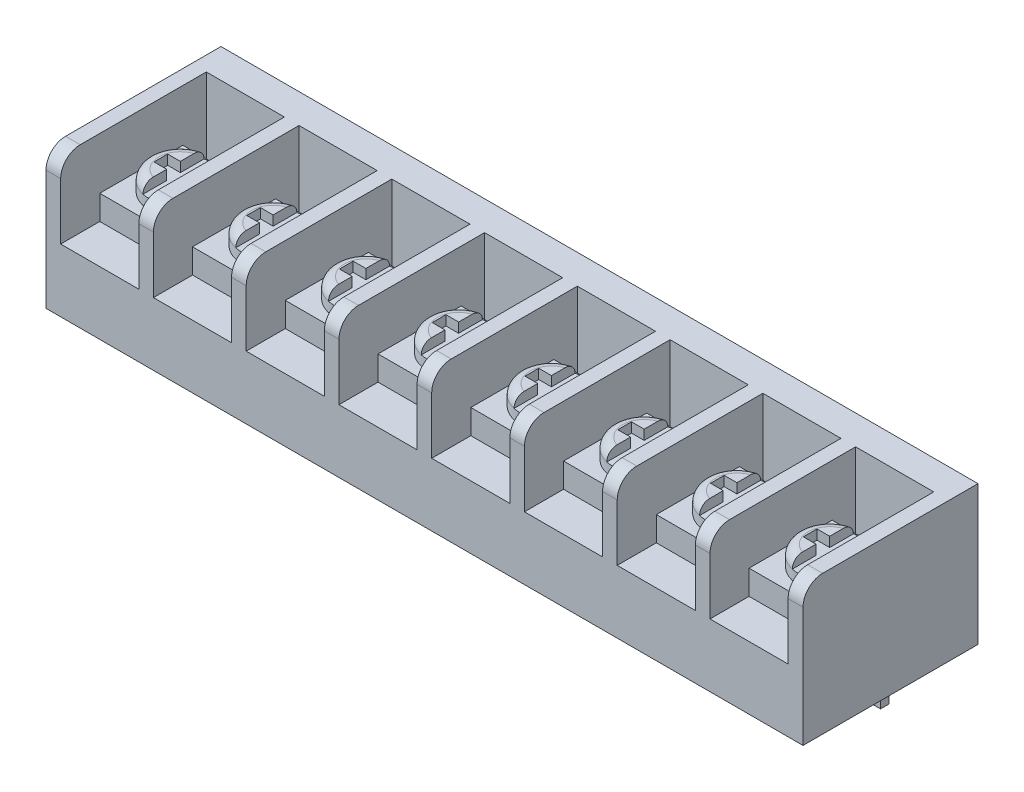
SolidWorks part; units mm, degrees
ref_plane "Front Plane" through (0, 0, 0) normal (0, 0, 1) x (1, 0, 0)
ref_plane "Top Plane" through (0, 0, 0) normal (0, 1, 0) x (1, 0, 0)
ref_plane "Right Plane" through (0, 0, 0) normal (1, 0, 0) x (0, 0, -1)
sketch "Sketch1" plane through (0, 0, 0) normal (0, 1, 0) x (1, 0, 0)
  line L1 (-38.725, 8.95) -> (38.725, 8.95)
  line L2 (-38.725, 8.95) -> (-38.725, -8.95)
  line L3 (-38.725, -8.95) -> (38.725, -8.95)
  line L4 (38.725, 8.95) -> (38.725, -8.95)
  line L5 (-38.725, 8.95) -> (38.725, -8.95) construction
  line L6 (-38.725, -8.95) -> (38.725, 8.95) construction
  point P0 (0, 0)
  dimension "D1" = 77.45
  dimension "D2" = 17.9
extrude "Boss-Extrude1" add sketch "Sketch1" along normal blind 14.25
fillet "Fillet1" radius 2 1 edges at (0, 14.25, 8.95)
sketch "Sketch2" plane through (0, 14.25, 0) normal (0, 1, 0) x (1, 0, 0)
  line L0 (-38.725, -8.95) -> (38.725, -8.95) construction
  line L1 (-37.225, 5.95) -> (-29.2312, 5.95)
  line L2 (-37.225, 5.95) -> (-37.225, -8.95)
  line L3 (-37.225, -8.95) -> (-29.2312, -8.95)
  line L4 (-29.2312, 5.95) -> (-29.2312, -8.95)
  line L5 (38.725, 8.95) -> (-38.725, 8.95) construction
  line L10 (-38.725, 8.95) -> (-38.725, -6.95) construction
  line L12 (-27.735, 5.95) -> (-27.735, -8.95)
  line L13 (-27.735, 5.95) -> (-19.7412, 5.95)
  line L14 (-19.7412, 5.95) -> (-19.7412, -8.95)
  line L15 (-27.735, -8.95) -> (-19.7412, -8.95)
  line L16 (-18.245, 5.95) -> (-18.245, -8.95)
  line L17 (-18.245, 5.95) -> (-10.2512, 5.95)
  line L18 (-10.2512, 5.95) -> (-10.2512, -8.95)
  line L19 (-18.245, -8.95) -> (-10.2512, -8.95)
  line L20 (-8.755, 5.95) -> (-8.755, -8.95)
  line L21 (-8.755, 5.95) -> (-0.7612, 5.95)
  line L22 (-0.7612, 5.95) -> (-0.7612, -8.95)
  line L23 (-8.755, -8.95) -> (-0.7612, -8.95)
  line L24 (0.735, 5.95) -> (0.735, -8.95)
  line L25 (0.735, 5.95) -> (8.7288, 5.95)
  line L26 (8.7288, 5.95) -> (8.7288, -8.95)
  line L27 (0.735, -8.95) -> (8.7288, -8.95)
  line L28 (10.225, 5.95) -> (10.225, -8.95)
  line L29 (10.225, 5.95) -> (18.2188, 5.95)
  line L30 (18.2188, 5.95) -> (18.2188, -8.95)
  line L31 (10.225, -8.95) -> (18.2188, -8.95)
  line L32 (19.715, 5.95) -> (19.715, -8.95)
  line L33 (19.715, 5.95) -> (27.7088, 5.95)
  line L34 (27.7088, 5.95) -> (27.7088, -8.95)
  line L35 (19.715, -8.95) -> (27.7088, -8.95)
  line L36 (29.205, 5.95) -> (29.205, -8.95)
  line L37 (29.205, 5.95) -> (37.1988, 5.95)
  line L38 (37.1988, 5.95) -> (37.1988, -8.95)
  line L39 (29.205, -8.95) -> (37.1988, -8.95)
  line L40 (-37.225, 5.95) -> (-27.735, 5.95) construction
  dimension "D1" = 3
  dimension "D2" = 1.5
  dimension "D3" = 7.9938
  dimension "D4" = 8
  dimension "D5" = 9.49
extrude "Cut-Extrude1" cut sketch "Sketch2" against normal blind 7.8
sketch "Sketch3" plane through (0, 0, 0) normal (0, -1, 0) x (1, 0, 0)
  line L1 (-33.8781, -3.85) -> (-32.5781, -3.85)
  line L2 (-33.8781, -3.85) -> (-33.8781, -4.7)
  line L3 (-33.8781, -4.7) -> (-32.5781, -4.7)
  line L4 (-32.5781, -3.85) -> (-32.5781, -4.7)
  line L9 (38.725, -8.95) -> (-38.725, -8.95) construction
  line L10 (-37.225, 8.95) -> (-29.2312, 8.95) construction
  line L11 (-24.3881, -3.85) -> (-24.3881, -4.7)
  line L12 (-24.3881, -3.85) -> (-23.0881, -3.85)
  line L13 (-23.0881, -3.85) -> (-23.0881, -4.7)
  line L14 (-24.3881, -4.7) -> (-23.0881, -4.7)
  line L15 (-14.8981, -3.85) -> (-14.8981, -4.7)
  line L16 (-14.8981, -3.85) -> (-13.5981, -3.85)
  line L17 (-13.5981, -3.85) -> (-13.5981, -4.7)
  line L18 (-14.8981, -4.7) -> (-13.5981, -4.7)
  line L19 (-5.4081, -3.85) -> (-5.4081, -4.7)
  line L20 (-5.4081, -3.85) -> (-4.1081, -3.85)
  line L21 (-4.1081, -3.85) -> (-4.1081, -4.7)
  line L22 (-5.4081, -4.7) -> (-4.1081, -4.7)
  line L23 (4.0819, -3.85) -> (4.0819, -4.7)
  line L24 (4.0819, -3.85) -> (5.3819, -3.85)
  line L25 (5.3819, -3.85) -> (5.3819, -4.7)
  line L26 (4.0819, -4.7) -> (5.3819, -4.7)
  line L27 (13.5719, -3.85) -> (13.5719, -4.7)
  line L28 (13.5719, -3.85) -> (14.8719, -3.85)
  line L29 (14.8719, -3.85) -> (14.8719, -4.7)
  line L30 (13.5719, -4.7) -> (14.8719, -4.7)
  line L31 (23.0619, -3.85) -> (23.0619, -4.7)
  line L32 (23.0619, -3.85) -> (24.3619, -3.85)
  line L33 (24.3619, -3.85) -> (24.3619, -4.7)
  line L34 (23.0619, -4.7) -> (24.3619, -4.7)
  line L35 (32.5519, -3.85) -> (32.5519, -4.7)
  line L36 (32.5519, -3.85) -> (33.8519, -3.85)
  line L37 (33.8519, -3.85) -> (33.8519, -4.7)
  line L38 (32.5519, -4.7) -> (33.8519, -4.7)
  line L39 (-33.8781, -3.85) -> (-24.3881, -3.85) construction
  point P6 (-33.2281, -3.85)
  point P11 (-33.2281, 8.95)
  dimension "D1" = 0.85
  dimension "D2" = 1.3
  dimension "D3" = 8
  dimension "D4" = 4.25
  dimension "D5" = 9.49
extrude "Boss-Extrude2" add sketch "Sketch3" along normal blind 5.6 separate body
sketch "Sketch4" plane through (0, 6.45, 0) normal (0, 1, 0) x (1, 0, 0)
  line L0 (-37.225, 5.95) -> (-37.225, -8.95) construction
  line L1 (-37.225, 3.55) -> (-29.2312, 3.55)
  line L2 (-37.225, 3.55) -> (-37.225, -4.95)
  line L3 (-37.225, -4.95) -> (-29.2312, -4.95)
  line L4 (-29.2312, 3.55) -> (-29.2312, -4.95)
  line L5 (-29.2312, -8.95) -> (-29.2312, 5.95) construction
  line L6 (-37.225, -8.95) -> (-29.2312, -8.95) construction
  line L13 (-27.735, 3.55) -> (-27.735, -4.95)
  line L14 (-27.735, 3.55) -> (-19.7412, 3.55)
  line L15 (-19.7412, 3.55) -> (-19.7412, -4.95)
  line L16 (-27.735, -4.95) -> (-19.7412, -4.95)
  line L17 (-18.245, 3.55) -> (-18.245, -4.95)
  line L18 (-18.245, 3.55) -> (-10.2512, 3.55)
  line L19 (-10.2512, 3.55) -> (-10.2512, -4.95)
  line L20 (-18.245, -4.95) -> (-10.2512, -4.95)
  line L21 (-8.755, 3.55) -> (-8.755, -4.95)
  line L22 (-8.755, 3.55) -> (-0.7612, 3.55)
  line L23 (-0.7612, 3.55) -> (-0.7612, -4.95)
  line L24 (-8.755, -4.95) -> (-0.7612, -4.95)
  line L25 (0.735, 3.55) -> (0.735, -4.95)
  line L26 (0.735, 3.55) -> (8.7288, 3.55)
  line L27 (8.7288, 3.55) -> (8.7288, -4.95)
  line L28 (0.735, -4.95) -> (8.7288, -4.95)
  line L29 (10.225, 3.55) -> (10.225, -4.95)
  line L30 (10.225, 3.55) -> (18.2188, 3.55)
  line L31 (18.2188, 3.55) -> (18.2188, -4.95)
  line L32 (10.225, -4.95) -> (18.2188, -4.95)
  line L33 (19.715, 3.55) -> (19.715, -4.95)
  line L34 (19.715, 3.55) -> (27.7088, 3.55)
  line L35 (27.7088, 3.55) -> (27.7088, -4.95)
  line L36 (19.715, -4.95) -> (27.7088, -4.95)
  line L37 (29.205, 3.55) -> (29.205, -4.95)
  line L38 (29.205, 3.55) -> (37.1988, 3.55)
  line L39 (37.1988, 3.55) -> (37.1988, -4.95)
  line L40 (29.205, -4.95) -> (37.1988, -4.95)
  line L41 (-37.225, 3.55) -> (-27.735, 3.55) construction
  dimension "D1" = 4
  dimension "D2" = 8.5
  dimension "D4" = 9.49
  dimension "D3" = 8
extrude "Boss-Extrude3" add sketch "Sketch4" along normal blind 2.5 separate body
sketch "Sketch5" plane through (0, 8.95, 0) normal (0, 1, 0) x (1, 0, 0)
  line L0 (-29.2312, 3.55) -> (-37.225, 3.55) construction
  line L3 (-37.225, 3.55) -> (-37.225, -4.95) construction
  line L4 (-33.2281, -0.7) -> (-23.7381, -0.7) construction
  circle A0 centre (-33.2281, -0.7) radius 3.2
  circle A2 centre (-23.7381, -0.7) radius 3.2
  circle A3 centre (-14.2481, -0.7) radius 3.2
  circle A4 centre (-4.7581, -0.7) radius 3.2
  circle A5 centre (4.7319, -0.7) radius 3.2
  circle A6 centre (14.2219, -0.7) radius 3.2
  circle A7 centre (23.7119, -0.7) radius 3.2
  circle A8 centre (33.2019, -0.7) radius 3.2
  point P6 (-33.2281, 3.55)
  point P15 (-37.225, -0.7)
  dimension "D1" = 6.4
  dimension "D3" = 9.49
  dimension "D2" = 8
extrude "Boss-Extrude4" add sketch "Sketch5" along normal blind 2
sketch "Sketch6" plane through (0, 10.95, 0) normal (0, 1, 0) x (1, 0, 0)
  line L0 (-33.9281, 2.5) -> (-33.9281, 0)
  line L1 (-33.9281, 0) -> (-35.2281, 0)
  line L2 (-35.2281, 0) -> (-35.2281, -1.4)
  line L3 (-35.2281, -1.4) -> (-33.9281, -1.4)
  line L4 (-33.9281, -1.4) -> (-33.9281, -3.9)
  line L5 (-33.9281, -3.9) -> (-32.5281, -3.9)
  line L6 (-32.5281, -3.9) -> (-32.5281, -1.4)
  line L7 (-32.5281, -1.4) -> (-31.2281, -1.4)
  line L8 (-31.2281, -1.4) -> (-31.2281, 0)
  line L9 (-31.2281, 0) -> (-32.5281, 0)
  line L10 (-32.5281, 0) -> (-32.5281, 2.5)
  line L11 (-32.5281, 2.5) -> (-33.9281, 2.5)
  line L12 (-23.0381, 2.5) -> (-24.4381, 2.5)
  line L25 (-24.4381, 2.5) -> (-24.4381, 0)
  line L26 (-24.4381, 0) -> (-25.7381, 0)
  line L27 (-25.7381, 0) -> (-25.7381, -1.4)
  line L28 (-25.7381, -1.4) -> (-24.4381, -1.4)
  line L29 (-24.4381, -1.4) -> (-24.4381, -3.9)
  line L30 (-24.4381, -3.9) -> (-23.0381, -3.9)
  line L31 (-23.0381, -3.9) -> (-23.0381, -1.4)
  line L32 (-23.0381, -1.4) -> (-21.7381, -1.4)
  line L33 (-21.7381, -1.4) -> (-21.7381, 0)
  line L34 (-21.7381, 0) -> (-23.0381, 0)
  line L35 (-23.0381, 0) -> (-23.0381, 2.5)
  line L36 (-13.5481, 2.5) -> (-14.9481, 2.5)
  line L37 (-14.9481, 2.5) -> (-14.9481, 0)
  line L38 (-14.9481, 0) -> (-16.2481, 0)
  line L39 (-16.2481, 0) -> (-16.2481, -1.4)
  line L40 (-16.2481, -1.4) -> (-14.9481, -1.4)
  line L41 (-14.9481, -1.4) -> (-14.9481, -3.9)
  line L42 (-14.9481, -3.9) -> (-13.5481, -3.9)
  line L43 (-13.5481, -3.9) -> (-13.5481, -1.4)
  line L44 (-13.5481, -1.4) -> (-12.2481, -1.4)
  line L45 (-12.2481, -1.4) -> (-12.2481, 0)
  line L46 (-12.2481, 0) -> (-13.5481, 0)
  line L47 (-13.5481, 0) -> (-13.5481, 2.5)
  line L48 (-4.0581, 2.5) -> (-5.4581, 2.5)
  line L49 (-5.4581, 2.5) -> (-5.4581, 0)
  line L50 (-5.4581, 0) -> (-6.7581, 0)
  line L51 (-6.7581, 0) -> (-6.7581, -1.4)
  line L52 (-6.7581, -1.4) -> (-5.4581, -1.4)
  line L53 (-5.4581, -1.4) -> (-5.4581, -3.9)
  line L54 (-5.4581, -3.9) -> (-4.0581, -3.9)
  line L55 (-4.0581, -3.9) -> (-4.0581, -1.4)
  line L56 (-4.0581, -1.4) -> (-2.7581, -1.4)
  line L57 (-2.7581, -1.4) -> (-2.7581, 0)
  line L58 (-2.7581, 0) -> (-4.0581, 0)
  line L59 (-4.0581, 0) -> (-4.0581, 2.5)
  line L60 (5.4319, 2.5) -> (4.0319, 2.5)
  line L61 (4.0319, 2.5) -> (4.0319, 0)
  line L62 (4.0319, 0) -> (2.7319, 0)
  line L63 (2.7319, 0) -> (2.7319, -1.4)
  line L64 (2.7319, -1.4) -> (4.0319, -1.4)
  line L65 (4.0319, -1.4) -> (4.0319, -3.9)
  line L66 (4.0319, -3.9) -> (5.4319, -3.9)
  line L67 (5.4319, -3.9) -> (5.4319, -1.4)
  line L68 (5.4319, -1.4) -> (6.7319, -1.4)
  line L69 (6.7319, -1.4) -> (6.7319, 0)
  line L70 (6.7319, 0) -> (5.4319, 0)
  line L71 (5.4319, 0) -> (5.4319, 2.5)
  line L72 (14.9219, 2.5) -> (13.5219, 2.5)
  line L73 (13.5219, 2.5) -> (13.5219, 0)
  line L74 (13.5219, 0) -> (12.2219, 0)
  line L75 (12.2219, 0) -> (12.2219, -1.4)
  line L76 (12.2219, -1.4) -> (13.5219, -1.4)
  line L77 (13.5219, -1.4) -> (13.5219, -3.9)
  line L78 (13.5219, -3.9) -> (14.9219, -3.9)
  line L79 (14.9219, -3.9) -> (14.9219, -1.4)
  line L80 (14.9219, -1.4) -> (16.2219, -1.4)
  line L81 (16.2219, -1.4) -> (16.2219, 0)
  line L82 (16.2219, 0) -> (14.9219, 0)
  line L83 (14.9219, 0) -> (14.9219, 2.5)
  line L84 (24.4119, 2.5) -> (23.0119, 2.5)
  line L85 (23.0119, 2.5) -> (23.0119, 0)
  line L86 (23.0119, 0) -> (21.7119, 0)
  line L87 (21.7119, 0) -> (21.7119, -1.4)
  line L88 (21.7119, -1.4) -> (23.0119, -1.4)
  line L89 (23.0119, -1.4) -> (23.0119, -3.9)
  line L90 (23.0119, -3.9) -> (24.4119, -3.9)
  line L91 (24.4119, -3.9) -> (24.4119, -1.4)
  line L92 (24.4119, -1.4) -> (25.7119, -1.4)
  line L93 (25.7119, -1.4) -> (25.7119, 0)
  line L94 (25.7119, 0) -> (24.4119, 0)
  line L95 (24.4119, 0) -> (24.4119, 2.5)
  line L96 (33.9019, 2.5) -> (32.5019, 2.5)
  line L97 (32.5019, 2.5) -> (32.5019, 0)
  line L98 (32.5019, 0) -> (31.2019, 0)
  line L99 (31.2019, 0) -> (31.2019, -1.4)
  line L100 (31.2019, -1.4) -> (32.5019, -1.4)
  line L101 (32.5019, -1.4) -> (32.5019, -3.9)
  line L102 (32.5019, -3.9) -> (33.9019, -3.9)
  line L103 (33.9019, -3.9) -> (33.9019, -1.4)
  line L104 (33.9019, -1.4) -> (35.2019, -1.4)
  line L105 (35.2019, -1.4) -> (35.2019, 0)
  line L106 (35.2019, 0) -> (33.9019, 0)
  line L107 (33.9019, 0) -> (33.9019, 2.5)
  line L108 (-32.5281, 2.5) -> (-23.0381, 2.5) construction
  circle A0 centre (-33.2281, -0.7) radius 3.2 construction
  point P11 (-33.2281, -0.7)
  point P14 (-33.2281, 2.5)
  point P16 (-35.2281, -0.7)
  dimension "D1" = 4
  dimension "D2" = 8
  dimension "D3" = 9.49
extrude "Cut-Extrude2" cut sketch "Sketch6" against normal blind 1
fillet "Fillet5" radius 1 2 edges at (-30.0281, 10.95, 0.7) (-36.4281, 10.95, 0.7)
fillet "Fillet6" radius 1 2 edges at (-20.5381, 10.95, 0.7) (-26.9381, 10.95, 0.7)
fillet "Fillet7" radius 1 2 edges at (-11.0481, 10.95, 0.7) (-17.4481, 10.95, 0.7)
fillet "Fillet8" radius 1 2 edges at (-1.5581, 10.95, 0.7) (-7.9581, 10.95, 0.7)
fillet "Fillet9" radius 1 2 edges at (7.9319, 10.95, 0.7) (1.5319, 10.95, 0.7)
fillet "Fillet10" radius 1 2 edges at (17.4219, 10.95, 0.7) (11.0219, 10.95, 0.7)
fillet "Fillet11" radius 1 2 edges at (26.9119, 10.95, 0.7) (20.5119, 10.95, 0.7)
fillet "Fillet12" radius 1 2 edges at (36.4019, 10.95, 0.7) (30.0019, 10.95, 0.7)
